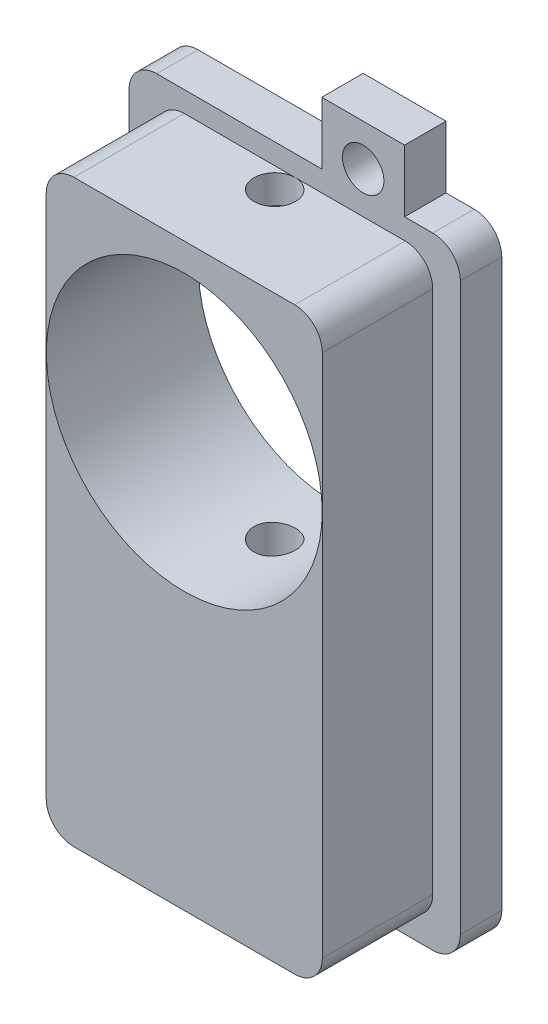
SolidWorks part; units mm, degrees
ref_plane "Front Plane" through (0, 0, 0) normal (0, 0, 1) x (1, 0, 0)
ref_plane "Top Plane" through (0, 0, 0) normal (0, 1, 0) x (1, 0, 0)
ref_plane "Right Plane" through (0, 0, 0) normal (1, 0, 0) x (0, 0, -1)
sketch "Sketch1" plane through (0, 0, 0) normal (0, 0, 1) x (1, 0, 0)
  line L0 (1.96, 22.5) -> (1.96, 27)
  line L1 (12, -22.5) -> (-12, -22.5)
  line L2 (12, -22.5) -> (12, 22.5)
  line L3 (12, 22.5) -> (-12, 22.5)
  line L4 (-12, -22.5) -> (-12, 22.5)
  line L5 (12, -22.5) -> (-12, 22.5) construction
  line L6 (12, 22.5) -> (-12, -22.5) construction
  line L7 (1.96, 27) -> (7.96, 27)
  line L8 (7.96, 27) -> (7.96, 22.5)
  line L9 (-7.96, -22.5) -> (-7.96, -27)
  line L10 (-7.96, -27) -> (-1.96, -27)
  line L11 (-1.96, -27) -> (-1.96, -22.5)
  circle A0 centre (4.96, 24) radius 1.5
  circle A1 centre (-4.96, -24) radius 1.5
  point P0 (0, 0)
  dimension "D6" = 3
  dimension "D11" = 3
  dimension "D1" = 24
  dimension "D2" = 45
  dimension "D3" = 4.04
  dimension "D4" = 6
  dimension "D5" = 4.5
  dimension "D7" = 1.5
  dimension "D8" = 6
  dimension "D9" = 4.5
  dimension "D10" = 4.04
  dimension "D12" = 1.5
  dimension "D13" = 3
  dimension "D14" = 3
extrude "Boss-Extrude1" add sketch "Sketch1" along normal blind 3 contours L4 L1 L2 L3 | L3 A0 L8 L7 L0 | L1 A1 L9 L10 L11
fillet "Fillet1" radius 2 4 edges at (12, -22.5, 1.5) (-12, -22.5, 1.5) (-12, 22.5, 1.5) (12, 22.5, 1.5)
sketch "Sketch3" plane through (0, 0, 3) normal (0, 0, 1) x (1, 0, 0)
  line L1 (10, -21) -> (-10, -21)
  line L2 (10, -21) -> (10, 21)
  line L3 (10, 21) -> (-10, 21)
  line L4 (-10, -21) -> (-10, 21)
  line L5 (10, -21) -> (-10, 21) construction
  line L6 (10, 21) -> (-10, -21) construction
  point P0 (0, 0)
  dimension "D1" = 20
  dimension "D2" = 42
extrude "Boss-Extrude2" add sketch "Sketch3" along normal blind 8
fillet "Fillet2" radius 2 4 edges at (10, -21, 7) (-10, -21, 7) (-10, 21, 7) (10, 21, 7)
sketch "Sketch4" plane through (0, 0, 11) normal (0, 0, 1) x (1, 0, 0)
  line L0 (8, 21) -> (-8, 21) construction
  circle A0 centre (0, 9) radius 9.99
  dimension "D1" = 19.98
  dimension "D2" = 12
extrude "Cut-Extrude1" cut sketch "Sketch4" against normal through all
sketch "Sketch5" plane through (0, 21, 0) normal (0, 1, 0) x (1, 0, 0)
  line L0 (1.96, -3) -> (1.96, 0) construction
  line L1 (1.96, -3) -> (7.96, -3) construction
  circle A0 centre (0.05, -4.5) radius 1.5
  dimension "D1" = 3
  dimension "D2" = 1.91
  dimension "D3" = 1.5
extrude "Cut-Extrude2" cut sketch "Sketch5" against normal through all
